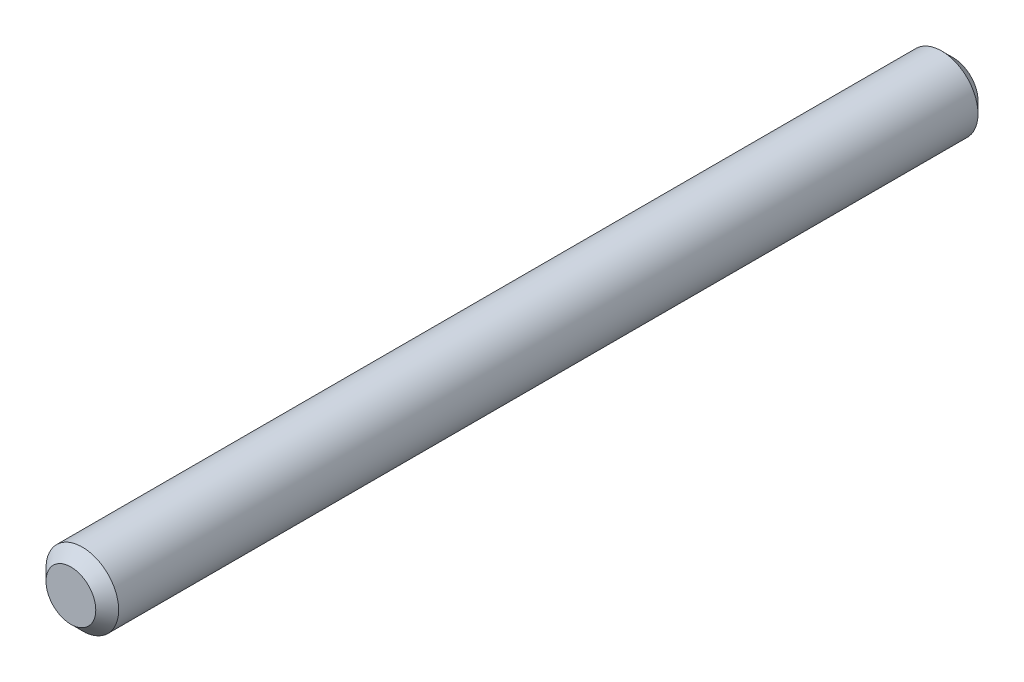
SolidWorks part; units mm, degrees
material "AISI 1020"
ref_plane "Front Plane" through (0, 0, 0) normal (0, 0, 1) x (1, 0, 0)
ref_plane "Top Plane" through (0, 0, 0) normal (0, 1, 0) x (1, 0, 0)
ref_plane "Right Plane" through (0, 0, 0) normal (1, 0, 0) x (0, 0, -1)
sketch "Sketch1" plane through (0, 0, 0) normal (0, 0, 1) x (1, 0, 0)
  circle A0 centre (0, 0) radius 3.175
  dimension "D1" = 6.35
extrude "Boss-Extrude1" add sketch "Sketch1" against normal blind 77.086
cosmetic thread "Cosmetic Thread1" parameters "D2"=5.268
chamfer "Chamfer1" distance 1 angle 45 2 edges at (3.175, 0, -77.086) (3.175, 0, 0)
